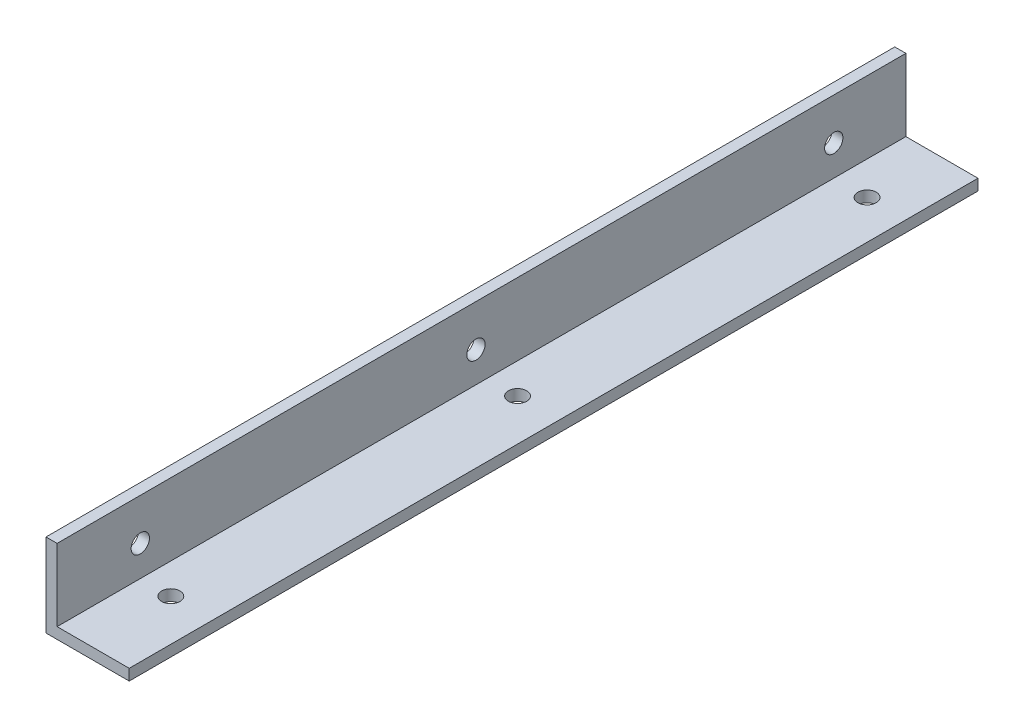
SolidWorks part; units mm, degrees
ref_plane "正面" through (0, 0, 0) normal (0, 0, 1) x (1, 0, 0)
ref_plane "平面" through (0, 0, 0) normal (0, 1, 0) x (1, 0, 0)
ref_plane "右側面" through (0, 0, 0) normal (1, 0, 0) x (0, 0, -1)
sketch "ｽｹｯﾁ1" plane through (0, 0, 0) normal (0, 0, 1) x (1, 0, 0)
  line L0 (0, 0) -> (0, 15)
  line L1 (0, 15) -> (2, 15)
  line L2 (2, 15) -> (2, 2)
  line L3 (2, 2) -> (15, 2)
  line L4 (15, 2) -> (15, 0)
  line L5 (15, 0) -> (0, 0)
  dimension "D1" = 15
  dimension "D2" = 15
  dimension "D3" = 2
  dimension "D4" = 2
extrude "ﾎﾞｽ - 押し出し1" add sketch "ｽｹｯﾁ1" along normal blind 155
sketch "ｽｹｯﾁ2" plane through (0, 2, 0) normal (0, 1, 0) x (1, 0, 0)
  line L0 (8, 0) -> (8, -15)
  line L1 (15, 0) -> (2, 0) construction
  line L2 (15, -155) -> (7.5, -155)
  line L3 (7.5, -155) -> (7.5, -140)
  line L4 (7.5, -155) -> (7.5, -77.5)
  line L5 (15, -155) -> (15, 0) construction
  line L6 (15, -155) -> (2, -155) construction
  circle A0 centre (8, -15) radius 2.2
  circle A1 centre (7.5, -140) radius 2.2
  circle A2 centre (7.5, -77.5) radius 2.2
  dimension "D2" = 4.4
  dimension "D4" = 15
  dimension "D6" = 4.4
  dimension "D8" = 4.4
  dimension "D1" = 15
  dimension "D3" = 7.5
  dimension "D5" = 7
  dimension "D7" = 77.5
sketch "ｽｹｯﾁ3" plane through (2, 0, 0) normal (1, 0, 0) x (0, 0, -1)
  line L0 (0, 15) -> (0, 7.5)
  line L1 (0, 2) -> (0, 15) construction
  line L2 (0, 7.5) -> (-15, 7.5)
  line L3 (-155, 15) -> (-155, 7.5)
  line L4 (-155, 2) -> (-155, 15) construction
  line L5 (-155, 7.5) -> (-140, 7.5)
  line L6 (-155, 7.5) -> (-79.5, 7.5)
  circle A0 centre (-15, 7.5) radius 2.2
  circle A1 centre (-140, 7.5) radius 2.2
  circle A2 centre (-79.5, 7.5) radius 2.2
  dimension "D3" = 4.4
  dimension "D5" = 4.4
  dimension "D7" = 4.4
  dimension "D1" = 7.5
  dimension "D2" = 15
  dimension "D4" = 15
  dimension "D6" = 75.5
hole_wizard "M4x0.7 ねじ穴1" positions "3Dｽｹｯﾁ1" profile "ｽｹｯﾁ4" tap size "M4x0.7" standard "JIS"
sketch3d "3Dｽｹｯﾁ1"
  point P0 (2, 7.5, 140)
  point P3 (7.5, 2, 140)
  point P6 (7.5, 2, 77.5)
  point P9 (2, 7.5, 79.5)
  point P12 (8, 2, 15)
  point P15 (2, 7.5, 15)
sketch "ｽｹｯﾁ4" plane through (2, 7.5, 140) normal (0, 1, 0) x (0, 0, -1)
  line L0 (0, 0) -> (0, 12.4914)
  line L1 (0, 12.4914) -> (1.65, 11.5)
  line L2 (1.65, 11.5) -> (1.65, 0)
  line L5 (1.65, 0) -> (0, 0)
  line L10 (0, 12.4914) -> (-1.65, 11.5) construction
  line L11 (0, -6.35) -> (0, 107.95) construction
  dimension "ねじ下穴ﾄﾞﾘﾙ直径" = 3.3
  dimension "ねじ下穴ﾄﾞﾘﾙの深さ" = 11.5
  dimension "ﾄﾞﾘﾙ角度" = 118
cosmetic thread "穴のねじ山1" parameters "D1"=2, "D2"=4
cosmetic thread "穴のねじ山2" parameters "D1"=2, "D2"=4
cosmetic thread "穴のねじ山3" parameters "D1"=2, "D2"=4
cosmetic thread "穴のねじ山4" parameters "D1"=2, "D2"=4
cosmetic thread "穴のねじ山5" parameters "D1"=2, "D2"=4
cosmetic thread "穴のねじ山6" parameters "D1"=2, "D2"=4
sketch "ｽｹｯﾁ6" plane through (0, 0, 0) normal (0, 0, -1) x (-1, 0, 0)
  line L1 (-18.2355, -5.3275) -> (6.3995, -5.3275)
  line L2 (-18.2355, -5.3275) -> (-18.2355, 29.0102)
  line L3 (-18.2355, 29.0102) -> (6.3995, 29.0102)
  line L4 (6.3995, -5.3275) -> (6.3995, 29.0102)
extrude "ｶｯﾄ - 押し出し2" cut sketch "ｽｹｯﾁ6" against normal blind 2
